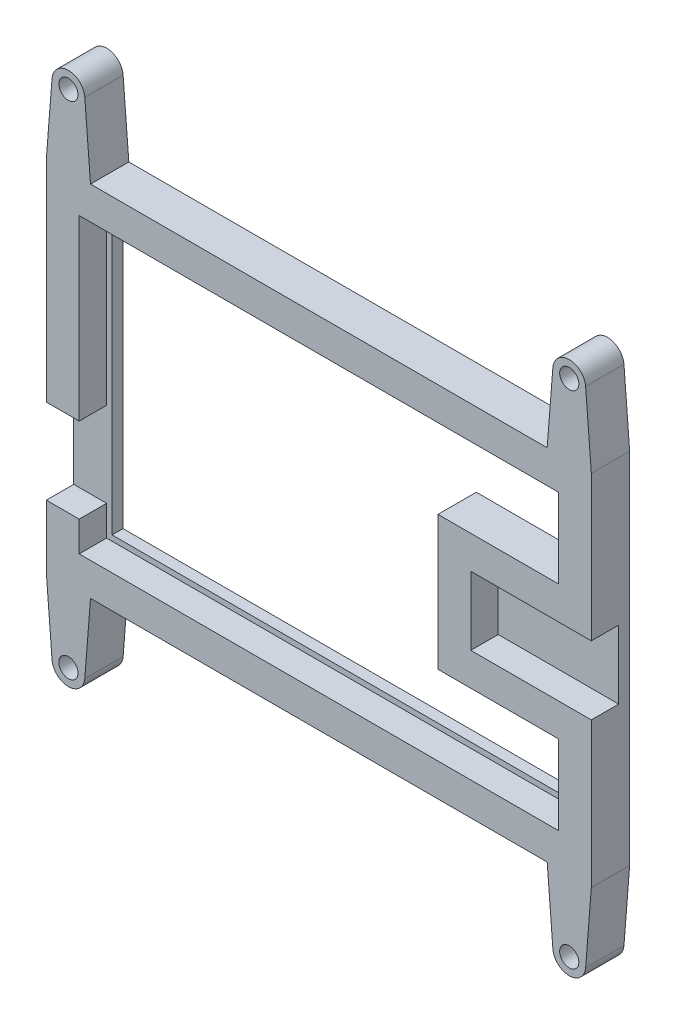
SolidWorks part; units mm, degrees
ref_plane "Front Plane" through (0, 0, 0) normal (0, 0, 1) x (1, 0, 0)
ref_plane "Top Plane" through (0, 0, 0) normal (0, 1, 0) x (1, 0, 0)
ref_plane "Right Plane" through (0, 0, 0) normal (1, 0, 0) x (0, 0, -1)
sketch "Sketch1" plane through (0, 0, 0) normal (0, 0, 1) x (1, 0, 0)
  line L1 (-43.75, 26.75) -> (43.75, 26.75)
  line L2 (-43.75, 26.75) -> (-43.75, -26.75)
  line L3 (-43.75, -26.75) -> (43.75, -26.75)
  line L4 (43.75, 26.75) -> (43.75, -26.75)
  line L5 (-43.75, 26.75) -> (43.75, -26.75) construction
  line L6 (-43.75, -26.75) -> (43.75, 26.75) construction
  line L7 (43.75, 12.25) -> (21.75, 12.25)
  line L8 (43.75, 12.25) -> (43.75, -12.25)
  line L9 (43.75, -12.25) -> (21.75, -12.25)
  line L10 (21.75, 12.25) -> (21.75, -12.25)
  point P0 (0, 0)
  point P10 (43.75, 0)
  dimension "D1" = 53.5
  dimension "D2" = 87.5
  dimension "D3" = 65.5
  dimension "D4" = 14.5
extrude "Boss-Extrude1" add sketch "Sketch1" along normal blind 5 contours L10 L7 L4 L1 L2 L3 L9
shell "Shell1" thickness 6
sketch "Sketch4" plane through (0, 0, 0) normal (0, 0, -1) x (-1, 0, 0)
  line L0 (43.75, 26.75) -> (43.75, -26.75) construction
  line L1 (49.75, 32.75) -> (-49.75, 32.75)
  line L2 (49.75, 32.75) -> (49.75, -32.75)
  line L3 (49.75, -32.75) -> (-49.75, -32.75)
  line L4 (-49.75, 32.75) -> (-49.75, -32.75)
  line L5 (-42.75, 25.75) -> (42.75, 25.75)
  line L6 (-42.75, 25.75) -> (-42.75, 12.25)
  line L7 (-42.75, -25.75) -> (42.75, -25.75)
  line L8 (42.75, 25.75) -> (42.75, -25.75)
  line L9 (-42.75, 25.75) -> (42.75, -25.75) construction
  line L10 (-42.75, -25.75) -> (42.75, 25.75) construction
  line L11 (43.75, -26.75) -> (-43.75, -26.75) construction
  line L12 (-43.75, 12.25) -> (-21.75, 12.25) construction
  line L13 (-21.75, -12.25) -> (-42.75, -12.25)
  line L14 (-21.75, -12.25) -> (-21.75, 12.25)
  line L15 (-21.75, 12.25) -> (-42.75, 12.25)
  line L17 (-42.75, -12.25) -> (-42.75, -25.75)
  point P4 (0, 0)
  dimension "D1" = 1
  dimension "D2" = 1
extrude "Boss-Extrude2" add sketch "Sketch4" along normal blind 2
sketch "Sketch5" plane through (0, 0, 5) normal (0, 0, 1) x (1, 0, 0)
  line L0 (-49.75, 32.75) -> (-49.75, -32.75) construction
  line L1 (-49.75, -5.75) -> (-43.75, -5.75)
  line L2 (-49.75, -5.75) -> (-49.75, -21.25)
  line L3 (-49.75, -21.25) -> (-43.75, -21.25)
  line L4 (-43.75, -5.75) -> (-43.75, -21.25)
  line L5 (-43.75, 26.75) -> (-43.75, -26.75) construction
  dimension "D1" = 5.5
  dimension "D2" = 15.5
extrude "Cut-Extrude2" cut sketch "Sketch5" against normal up to surface (5 mm away) up to face at (14.4167, 0, 0)
sketch "Sketch7" plane through (0, 0, -2) normal (0, 0, -1) x (-1, 0, 0)
  line L1 (-45.72, 45.72) -> (45.72, 45.72) construction
  line L2 (-45.72, 45.72) -> (-45.72, -45.72) construction
  line L3 (-45.72, -45.72) -> (45.72, -45.72) construction
  line L4 (45.72, 45.72) -> (45.72, -45.72) construction
  line L5 (-45.72, 45.72) -> (45.72, -45.72) construction
  line L6 (-45.72, -45.72) -> (45.72, 45.72) construction
  circle A0 centre (-45.72, 45.72) radius 1.75
  circle A1 centre (-45.72, 45.72) radius 3
  circle A2 centre (45.72, 45.72) radius 3
  circle A3 centre (45.72, 45.72) radius 1.75
  circle A4 centre (45.72, -45.72) radius 3
  circle A5 centre (45.72, -45.72) radius 1.75
  circle A6 centre (-45.72, -45.72) radius 3
  circle A7 centre (-45.72, -45.72) radius 1.75
  point P0 (0, 0)
  dimension "D3" = 3.5
  dimension "D4" = 6
  dimension "D1" = 91.44
  dimension "D2" = 91.44
  dimension "D5" = 2
  dimension "D6" = 2
extrude "Boss-Extrude3" add sketch "Sketch7" against normal up to surface (7 mm away) separate body up to face at (4.95, -2.7, 5)
sketch "Sketch8" plane through (0, 0, -2) normal (0, 0, -1) x (-1, 0, 0)
  line L0 (-49.75, 32.75) -> (-48.7108, 45.9554)
  line L1 (-42.7292, 45.9554) -> (-41.69, 32.75)
  line L2 (49.75, 32.75) -> (-49.75, 32.75) construction
  line L3 (-49.75, 32.75) -> (-41.69, 32.75)
  line L4 (48.7108, 45.9554) -> (49.75, 32.75)
  line L5 (41.69, 32.75) -> (42.7292, 45.9554)
  line L6 (41.69, 32.75) -> (49.75, 32.75)
  line L7 (0, 0) -> (49.75, 0) construction
  line L8 (49.75, 32.75) -> (49.75, -32.75) construction
  line L9 (41.69, -32.75) -> (49.75, -32.75)
  line L10 (41.69, -32.75) -> (42.7292, -45.9554)
  line L11 (-49.75, -32.75) -> (-41.69, -32.75)
  line L12 (-49.75, -32.75) -> (-48.7108, -45.9554)
  line L13 (-42.7292, -45.9554) -> (-41.69, -32.75)
  line L14 (48.7108, -45.9554) -> (49.75, -32.75)
  circle A0 centre (-45.72, 45.72) radius 3
  circle A1 centre (-45.72, 45.72) radius 3 construction
  circle A2 centre (-45.72, 45.72) radius 1.75
  circle A3 centre (-45.72, 45.72) radius 1.75 construction
  circle A4 centre (45.72, 45.72) radius 1.75
  circle A5 centre (45.72, 45.72) radius 3
  circle A6 centre (45.72, -45.72) radius 3
  circle A7 centre (45.72, -45.72) radius 1.75
  circle A8 centre (-45.72, -45.72) radius 3
  circle A9 centre (-45.72, -45.72) radius 1.75
  line M21 (49.75, 32.75) -> (-49.75, 32.75)
  line M23 (-49.75, -32.75) -> (49.75, -32.75)
  dimension "D1" = 8.06
  dimension "D2" = 2
extrude "Boss-Extrude4" add sketch "Sketch8" against normal up to surface (7 mm away) contours A0 L0 L1 M21 | A5 L5 L4 M21 | L10 A6 L14 M23 | L12 A8 L13 M23 up to face at (4.95, -2.7, 5)
